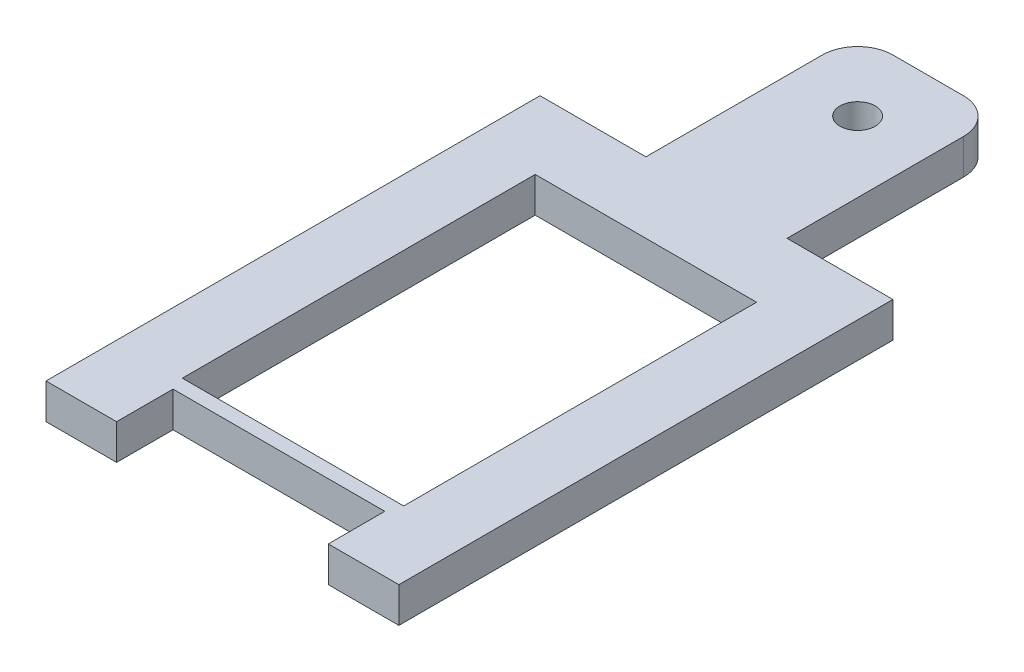
SolidWorks part; units mm, degrees
ref_plane "Front Plane" through (0, 0, 0) normal (0, 0, 1) x (1, 0, 0)
ref_plane "Top Plane" through (0, 0, 0) normal (0, 1, 0) x (1, 0, 0)
ref_plane "Right Plane" through (0, 0, 0) normal (1, 0, 0) x (0, 0, -1)
sketch "Sketch1" plane through (0, 0, 0) normal (0, 1, 0) x (1, 0, 0)
  line L0 (0, 8.89) -> (0, -8.89) construction
  line L2 (6.35, -8.89) -> (6.35, 8.89)
  line L4 (-6.35, -8.89) -> (-6.35, 8.89)
  line L5 (6.35, -8.89) -> (-6.35, 8.89) construction
  line L6 (6.35, 8.89) -> (-6.35, -8.89) construction
  line L7 (3.983, -6.35) -> (-3.983, -6.35)
  line L8 (3.983, -6.35) -> (3.983, 6.35)
  line L9 (3.983, 6.35) -> (-3.983, 6.35)
  line L10 (-3.983, -6.35) -> (-3.983, 6.35)
  line L11 (3.983, -6.35) -> (-3.983, 6.35) construction
  line L12 (3.983, 6.35) -> (-3.983, -6.35) construction
  line L13 (-3.81, -6.858) -> (3.81, -6.858)
  line L14 (-3.81, -6.858) -> (-3.81, -8.89)
  line L15 (-3.81, -8.89) -> (-6.35, -8.89)
  line L16 (3.81, -6.858) -> (3.81, -8.89)
  line L17 (3.81, -8.89) -> (6.35, -8.89)
  line L18 (2.54, 8.89) -> (-2.54, 8.89) construction
  line L19 (-2.54, 8.89) -> (-6.35, 8.89)
  line L20 (2.54, 8.89) -> (6.35, 8.89)
  line L21 (-2.54, 8.89) -> (-2.54, 15.24)
  line L22 (2.54, 8.89) -> (2.54, 15.24)
  line L23 (-1.27, 16.51) -> (1.27, 16.51)
  arc A0 (2.54, 15.24) -> (1.27, 16.51) centre (1.27, 15.24) ccw
  arc A1 (-2.54, 15.24) -> (-1.27, 16.51) centre (-1.27, 15.24) cw
  circle A2 centre (0, 13.97) radius 0.635
  point P0 (0, 0)
  point P6 (0, 0)
  point P16 (0, -6.858)
  point P21 (0, 8.89)
  point P27 (-2.54, 16.51)
  point P30 (0, 6.35)
  dimension "D8" = 1.27
  dimension "D9" = 1.27
  dimension "D1" = 17.78
  dimension "D2" = 12.7
  dimension "D3" = 5.08
  dimension "D4" = 12.7
  dimension "D5" = 7.62
  dimension "D6" = 2.032
  dimension "D7" = 7.62
  dimension "D10" = 7.62
extrude "Boss-Extrude1" add sketch "Sketch1" along normal blind 1.27
